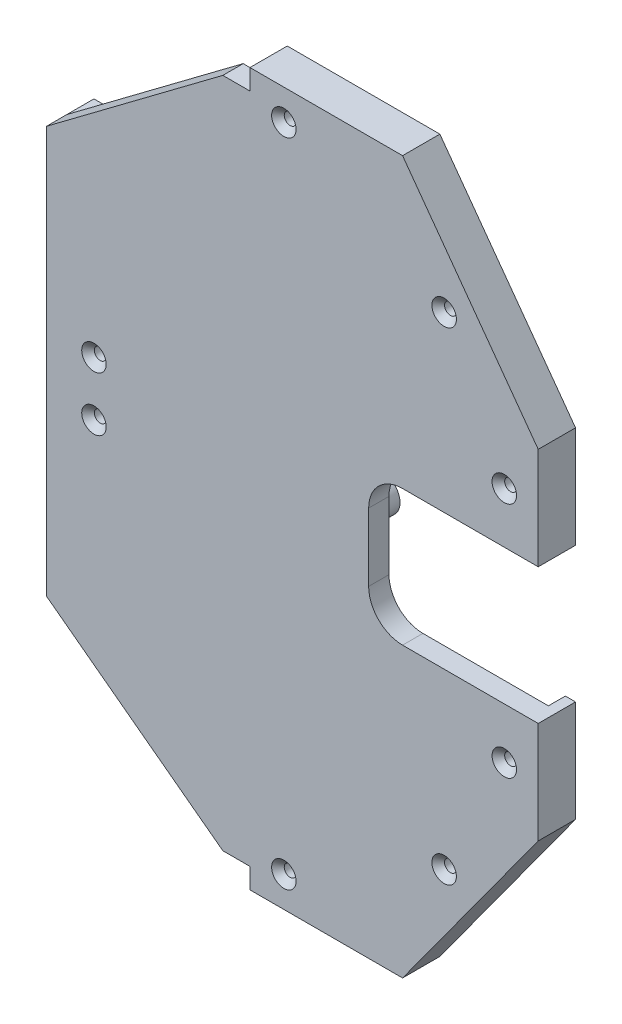
SolidWorks part; units mm, degrees
material "ABS PC"
ref_plane "Piano frontale" through (0, 0, 0) normal (0, 0, 1) x (1, 0, 0)
ref_plane "Piano superiore" through (0, 0, 0) normal (0, 1, 0) x (1, 0, 0)
ref_plane "Piano destro" through (0, 0, 0) normal (1, 0, 0) x (0, 0, -1)
sketch "Schizzo1" plane through (0, 0, 0) normal (0, 0, 1) x (1, 0, 0)
  line L0 (-8, -60) -> (-8, 60)
  line L1 (-8, 60) -> (52, 105)
  line L2 (52, 105) -> (97, 105)
  line L3 (97, 105) -> (137, 50)
  line L4 (137, 50) -> (137, -50)
  line L5 (0, 0) -> (30.0223, 0) construction
  line L6 (97, -105) -> (137, -50)
  line L7 (52, -105) -> (97, -105)
  line L8 (-8, -60) -> (52, -105)
  point P11 (137, 0)
  point P14 (-8, 0)
  dimension "D1" = 60
  dimension "D2" = 45
  dimension "D3" = 60
  dimension "D4" = 45
  dimension "D5" = 40
  dimension "D6" = 55
  dimension "D7" = 100
  dimension "D8" = 8
extrude "Estrusione-Estrusione2" add sketch "Schizzo1" along normal blind 6
shell "Svuota1" [suppressed] thickness 6
sketch "Schizzo2" plane through (0, 0, 0) normal (0, 0, -1) x (-1, 0, 0)
  line L6 (8, -60) -> (-17, -60)
  line L7 (8, -60) -> (8, -24)
  line L8 (8, -24) -> (-17, -24)
  line L9 (-17, -60) -> (-17, -24)
  line L10 (8, 60) -> (-17, 60)
  line L11 (8, 60) -> (8, 24)
  line L12 (8, 24) -> (-17, 24)
  line L13 (-17, 60) -> (-17, 24)
  dimension "D1" = 25
  dimension "D2" = 25
  dimension "D3" = 36
  dimension "D4" = 36
extrude "Estrusione-Estrusione3" add sketch "Schizzo2" along normal blind 8
sketch "Schizzo3" plane through (0, 0, 6) normal (0, 0, -1) x (-1, 0, 0)
  line L0 (-52, 105) -> (-44, 99)
  line L1 (-44, 99) -> (-52, 99)
  line L3 (-52, 99) -> (-52, 105)
  line L4 (-52, -105) -> (-44, -99)
  line L5 (-44, -99) -> (-52, -99)
  line L7 (-52, -99) -> (-52, -105)
  dimension "D1" = 6
  dimension "D2" = 8
  dimension "D3" = 6
  dimension "D4" = 8
extrude "Taglio-Estrusione1" cut sketch "Schizzo3" along normal through all
sketch "Schizzo4" plane through (0, 0, -8) normal (0, 0, -1) x (-1, 0, 0)
  line L0 (2.85, 30.0133) -> (2.85, 31.8867)
  line L1 (2.85, -30.0133) -> (2.85, -31.8867)
  arc A0 (2.85, 31.8867) -> (2.85, 30.0133) centre (0, 30.95) ccw
  arc A1 (2.85, -30.0133) -> (2.85, -31.8867) centre (0, -30.95) ccw
  dimension "D1" = 6
  dimension "D2" = 6
  dimension "D3" = 30.95
  dimension "D4" = 30.95
  dimension "D5" = 2.85
  dimension "D6" = 2.85
extrude "Taglio-Estrusione2" cut sketch "Schizzo4" against normal blind 10.5
sketch "Schizzo5" [suppressed] plane through (0, 0, 9) normal (0, 0, -1) x (-1, 0, 0)
  line L0 (-52, -99) -> (-93.9447, -99) construction
  line L1 (-93.9447, -99) -> (-131, -48.0489) construction
  line L2 (-131, -48.0489) -> (-131, 48.0489) construction
  line L3 (-131, 48.0489) -> (-93.9447, 99) construction
  line L4 (-93.9447, 99) -> (-52, 99) construction
  line L5 (-58, -99) -> (-66, -99)
  line L6 (-110.0355, -76.8751) -> (-114.7458, -70.3984)
  line L7 (-131, -39) -> (-131, -31)
  line L8 (-114.7458, 70.3984) -> (-110.0355, 76.8751)
  line L9 (-66, 99) -> (-58, 99)
  line L10 (-52, -99) -> (-52, -105) construction
  line L11 (-66, 95) -> (-66, 99)
  line L12 (-58, 95) -> (-58, 99)
  line L13 (-106.7654, 74.2608) -> (-110.0355, 76.8751)
  line L14 (-111.7607, 68.0121) -> (-114.7458, 70.3984)
  line L15 (-127, 39) -> (-131, 39)
  line L16 (-127, 31) -> (-131, 31)
  line L17 (-127, -31) -> (-131, -31)
  line L18 (-127, -39) -> (-131, -39)
  line L19 (-106.7654, -74.2608) -> (-110.0355, -76.8751)
  line L20 (-111.7607, -68.0121) -> (-114.7458, -70.3984)
  line L21 (-66, -95) -> (-66, -99)
  line L22 (-58, -95) -> (-58, -99)
  line L23 (-131, 31) -> (-131, 39)
  arc A0 (-66, 95) -> (-58, 95) centre (-62, 95) ccw
  arc A1 (-111.7607, 68.0121) -> (-106.7654, 74.2608) centre (-109.2631, 71.1365) ccw
  arc A2 (-127, 31) -> (-127, 39) centre (-127, 35) ccw
  arc A3 (-127, -39) -> (-127, -31) centre (-127, -35) ccw
  arc A4 (-106.7654, -74.2608) -> (-111.7607, -68.0121) centre (-109.2631, -71.1365) ccw
  arc A5 (-58, -95) -> (-66, -95) centre (-62, -95) ccw
  dimension "D1" = 8
  dimension "D5" = 8
  dimension "D7" = 4
  dimension "D9" = 15.3184
  dimension "D8" = 8
  dimension "D10" = 4
  dimension "D11" = 35
  dimension "D12" = 8
  dimension "D13" = 4
  dimension "D14" = 35
  dimension "D16" = 15.3184
  dimension "D17" = 8
  dimension "D18" = 4
  dimension "D19" = 8
  dimension "D20" = 10
  dimension "D2" = 41.9447
  dimension "D3" = 10
  dimension "D4" = 4
  dimension "D6" = 63.0009
  dimension "D15" = 4
extrude "Estrusione-Estrusione4" [suppressed] add sketch "Schizzo5" along normal up to surface (9 mm away)
sketch "Schizzo6" plane through (0, 0, 0) normal (0, 0, -1) x (-1, 0, 0)
  line L0 (-65, 0) -> (-75, 0) construction
  line L1 (-65, -3.25) -> (-75, -3.25)
  line L2 (-65, 3.25) -> (-75, 3.25)
  line L3 (-65, -5.25) -> (-75, -5.25)
  line L4 (-65, 5.25) -> (-75, 5.25)
  line L5 (-97.1925, 53.28) -> (-99.5884, 53.28)
  line L6 (-101.5884, 51.28) -> (-101.5884, 45.28)
  line L7 (-99.5884, 43.28) -> (-88.3384, 43.28)
  line L8 (-86.3384, 45.28) -> (-86.3384, 46.5885)
  line L9 (-87.7059, 48.4858) -> (-92.0679, 49.9399)
  line L10 (-97.1925, -53.28) -> (-99.5884, -53.28)
  line L11 (-101.5884, -51.28) -> (-101.5884, -45.28)
  line L12 (-99.5884, -43.28) -> (-88.3384, -43.28)
  line L13 (-86.3384, -45.28) -> (-86.3384, -46.5885)
  line L14 (-87.7059, -48.4858) -> (-92.0679, -49.9399)
  line L20 (-75.2704, -92.5997) -> (-79.6325, -94.0537)
  line L21 (-81, -95.951) -> (-81, -96.9595)
  line L22 (-79, -98.9595) -> (-71, -98.9595)
  line L23 (-67, -94.9595) -> (-67, -91.2595)
  line L24 (-69, -89.2595) -> (-70.1459, -89.2595)
  line L25 (-70.1459, 89.2595) -> (-69, 89.2595)
  line L26 (-67, 91.2595) -> (-67, 94.9595)
  line L27 (-71, 98.9595) -> (-79, 98.9595)
  line L28 (-81, 96.9595) -> (-81, 95.951)
  line L29 (-79.6325, 94.0537) -> (-75.2704, 92.5997)
  arc A0 (-65, -3.25) -> (-65, 3.25) centre (-65, 0) ccw
  arc A1 (-75, 3.25) -> (-75, -3.25) centre (-75, 0) ccw
  arc A2 (-75, 5.25) -> (-75, -5.25) centre (-75, 0) ccw
  arc A3 (-65, -5.25) -> (-65, 5.25) centre (-65, 0) ccw
  arc A4 (-75, 89.2595) -> (-92.3384, 53.28) centre (0, 30.95) ccw construction
  arc A5 (-77.5658, 91.2543) -> (-95.4973, 54.0439) centre (0, 30.95) ccw construction
  arc A6 (-72.4342, 87.2647) -> (-89.1794, 52.5161) centre (0, 30.95) ccw construction
  arc A7 (-72.4342, 87.2647) -> (-77.5658, 91.2543) centre (-75, 89.2595) ccw construction
  arc A8 (-95.4973, 54.0439) -> (-89.1794, 52.5161) centre (-92.3384, 53.28) ccw construction
  arc A9 (-95.3433, 52.0419) -> (-92.5625, 50.0377) centre (-92.3384, 53.28) ccw
  arc A10 (-79.1447, 92.4819) -> (-97.4413, 54.514) centre (0, 30.95) ccw construction
  arc A11 (-97.4413, 54.514) -> (-87.2354, 52.046) centre (-92.3384, 53.28) ccw construction
  arc A12 (-70.8553, 86.0372) -> (-87.2354, 52.046) centre (0, 30.95) ccw construction
  arc A13 (-70.8553, 86.0372) -> (-79.1447, 92.4819) centre (-75, 89.2595) ccw construction
  arc A14 (-75, -89.2595) -> (-92.3384, -53.28) centre (0, -30.95) cw construction
  arc A15 (-95.3433, 52.0419) -> (-97.1925, 53.28) centre (-97.1925, 51.28) ccw
  arc A16 (-99.5884, 53.28) -> (-101.5884, 51.28) centre (-99.5884, 51.28) ccw
  arc A21 (-95.4973, -54.0439) -> (-77.5658, -91.2543) centre (0, -30.95) ccw construction
  arc A22 (-89.1794, -52.5161) -> (-72.4342, -87.2647) centre (0, -30.95) ccw construction
  arc A23 (-89.1794, -52.5161) -> (-95.4973, -54.0439) centre (-92.3384, -53.28) ccw construction
  arc A24 (-77.5658, -91.2543) -> (-72.4342, -87.2647) centre (-75, -89.2595) ccw construction
  arc A25 (-97.4413, -54.514) -> (-79.1447, -92.4819) centre (0, -30.95) ccw construction
  arc A26 (-79.1447, -92.4819) -> (-70.8553, -86.0372) centre (-75, -89.2595) ccw construction
  arc A27 (-87.2354, -52.046) -> (-70.8553, -86.0372) centre (0, -30.95) ccw construction
  arc A28 (-87.2354, -52.046) -> (-97.4413, -54.514) centre (-92.3384, -53.28) ccw construction
  arc A29 (-101.5884, 45.28) -> (-99.5884, 43.28) centre (-99.5884, 45.28) ccw
  arc A30 (-88.3384, 43.28) -> (-86.3384, 45.28) centre (-88.3384, 45.28) ccw
  arc A31 (-86.3384, 46.5885) -> (-87.7059, 48.4858) centre (-88.3384, 46.5885) ccw
  arc A32 (-92.5625, 50.0377) -> (-92.0679, 49.9399) centre (-92.7004, 48.0425) cw
  arc A33 (-95.3433, -52.0419) -> (-92.5625, -50.0377) centre (-92.3384, -53.28) cw
  arc A34 (-88.3384, -43.28) -> (-86.3384, -45.28) centre (-88.3384, -45.28) cw
  arc A35 (-86.3384, -46.5885) -> (-87.7059, -48.4858) centre (-88.3384, -46.5885) cw
  arc A36 (-92.5625, -50.0377) -> (-92.0679, -49.9399) centre (-92.7004, -48.0425) ccw
  arc A37 (-95.3433, -52.0419) -> (-97.1925, -53.28) centre (-97.1925, -51.28) cw
  arc A38 (-99.5884, -53.28) -> (-101.5884, -51.28) centre (-99.5884, -51.28) cw
  arc A39 (-101.5884, -45.28) -> (-99.5884, -43.28) centre (-99.5884, -45.28) cw
  arc A47 (-71.9951, -90.4976) -> (-74.7759, -92.5018) centre (-75, -89.2595) cw
  arc A48 (-71, -98.9595) -> (-67, -94.9595) centre (-71, -94.9595) ccw
  arc A49 (-67, -91.2595) -> (-69, -89.2595) centre (-69, -91.2595) ccw
  arc A50 (-71.9951, -90.4976) -> (-70.1459, -89.2595) centre (-70.1459, -91.2595) cw
  arc A51 (-74.7759, -92.5018) -> (-75.2704, -92.5997) centre (-74.6379, -94.497) ccw
  arc A52 (-79.6325, -94.0537) -> (-81, -95.951) centre (-79, -95.951) ccw
  arc A53 (-81, -96.9595) -> (-79, -98.9595) centre (-79, -96.9595) ccw
  arc A54 (-71.9951, 90.4976) -> (-74.7759, 92.5018) centre (-75, 89.2595) ccw
  arc A55 (-69, 89.2595) -> (-67, 91.2595) centre (-69, 91.2595) ccw
  arc A56 (-71.9951, 90.4976) -> (-70.1459, 89.2595) centre (-70.1459, 91.2595) ccw
  arc A57 (-79, 98.9595) -> (-81, 96.9595) centre (-79, 96.9595) ccw
  arc A58 (-81, 95.951) -> (-79.6325, 94.0537) centre (-79, 95.951) ccw
  arc A59 (-74.7759, 92.5018) -> (-75.2704, 92.5997) centre (-74.6379, 94.497) cw
  arc A60 (-67, 94.9595) -> (-71, 98.9595) centre (-71, 94.9595) ccw
  point P3 (-70, 0)
  point P18 (-85.5813, 72.1912)
  point P36 (-85.5813, -72.1912)
  point P57 (-95.5884, 53.28)
  point P60 (-101.5884, 53.28)
  point P63 (-101.5884, 43.28)
  point P68 (-86.3384, 48.03)
  point P71 (-92.3384, 50.03)
  point P83 (-86.3384, -48.03)
  point P86 (-92.3384, -50.03)
  point P89 (-95.5884, -53.28)
  point P92 (-101.5884, -53.28)
  point P95 (-101.5884, -43.28)
  point P106 (-71.75, 89.2595)
  point P111 (-77.5617, 91.2595)
  point P112 (-81, 94.5095)
  point P115 (-75, 92.5095)
  point P132 (-71.75, -89.2595)
  point P135 (-75, -92.5095)
  point P138 (-81, -94.5095)
  dimension "D5" = 95
  dimension "D6" = 6.5
  dimension "D10" = 95
  dimension "D13" = 75
  dimension "D11" = 6.5
  dimension "D15" = 6
  dimension "D19" = 2
  dimension "D20" = 10
  dimension "D24" = 2
  dimension "D25" = 9.7
  dimension "D29" = 2
  dimension "D30" = 4
  dimension "D31" = 9.7
  dimension "D35" = 4
  dimension "D36" = 2
  dimension "D1" = 75
  dimension "D2" = 65
  dimension "D3" = 6.5
  dimension "D7" = 75
  dimension "D8" = 22.33
  dimension "D12" = 22.33
  dimension "D16" = 2
  dimension "D17" = 10
  dimension "D18" = 6
  dimension "D21" = 6
  dimension "D22" = 6
  dimension "D23" = 2
  dimension "D26" = 8
  dimension "D27" = 2
  dimension "D28" = 6
  dimension "D32" = 8
  dimension "D33" = 6
  dimension "D34" = 2
  dimension "D4" = 2
  dimension "D9" = 2
  dimension "D14" = 2
extrude "Estrusione-Estrusione5" add sketch "Schizzo6" along normal blind 10
sketch "Schizzo7" plane through (0, 0, 0) normal (0, 0, -1) x (-1, 0, 0)
  line L0 (-52, -105) -> (-97, -105) construction
  line L1 (-97, -105) -> (-137, -50) construction
  line L2 (-137, -50) -> (-137, 50) construction
  line L3 (-137, 50) -> (-97, 105) construction
  line L4 (-97, 105) -> (-52, 105) construction
  line L5 (-52, -105) -> (-97, -105)
  line L6 (-97, -105) -> (-137, -50)
  line L7 (-137, -50) -> (-137, 50)
  line L8 (-137, 50) -> (-97, 105)
  line L9 (-97, 105) -> (-52, 105)
  line L10 (-52, -102) -> (-95.4723, -102)
  line L11 (-95.4723, -102) -> (-134, -49.0244)
  line L12 (-134, -49.0244) -> (-134, 49.0244)
  line L13 (-134, 49.0244) -> (-95.4723, 102)
  line L14 (-95.4723, 102) -> (-52, 102)
  line L15 (-52, -102) -> (-52, -105)
  line L16 (-52, 105) -> (-52, 102)
  dimension "D1" = 3
extrude "Estrusione-Estrusione6" add sketch "Schizzo7" along normal blind 5
sketch "Schizzo8" plane through (0, 0, 6) normal (0, 0, 1) x (1, 0, 0)
  line L0 (137, -50) -> (137, 50) construction
  line L1 (137, 20) -> (97, 20)
  line L2 (137, 20) -> (137, -20)
  line L3 (137, -20) -> (97, -20)
  line L4 (87, 10) -> (87, -10)
  line L5 (52, 105) -> (52, 99) construction
  line L6 (137, 50) -> (97, 105) construction
  line L7 (97, 105) -> (52, 105) construction
  line L9 (52, -99) -> (52, -105) construction
  line L10 (97, -105) -> (137, -50) construction
  arc A0 (97, -20) -> (87, -10) centre (97, -10) cw
  arc A1 (97, 20) -> (87, 10) centre (97, 10) ccw
  arc A13 (58, 96) -> (66, 96) centre (62, 96) ccw construction
  circle A14 centre (62, 96) radius 1.75
  circle A15 centre (109.2631, 71.1365) radius 1.75
  circle A16 centre (127, 35) radius 1.75
  circle A17 centre (127, -35) radius 1.75
  circle A18 centre (109.2631, -71.1365) radius 1.75
  circle A19 centre (62, -96) radius 1.75
  circle A22 centre (6, -8) radius 1.75
  circle A23 centre (6, 8) radius 1.75
  point P11 (87, 20)
  dimension "D4" = 10
  dimension "D5" = 3.5
  dimension "D6" = 3.5
  dimension "D7" = 3.5
  dimension "D8" = 3.5
  dimension "D9" = 3.5
  dimension "D10" = 3.5
  dimension "D11" = 3.5
  dimension "D12" = 3.5
  dimension "D1" = 20
  dimension "D2" = 40
  dimension "D3" = 50
  dimension "D13" = 8
  dimension "D14" = 8
  dimension "D15" = 6
  dimension "D16" = 6
  dimension "D17" = 10
  dimension "D18" = 3
  dimension "D19" = 10
  dimension "D20" = 33.8635
  dimension "D21" = 10
  dimension "D22" = 35
  dimension "D23" = 35
  dimension "D24" = 10
  dimension "D25" = 3
  dimension "D26" = 10
  dimension "D27" = 10
  dimension "D28" = 33.8635
extrude "Taglio-Estrusione3" cut sketch "Schizzo8" against normal through all
sketch "Schizzo9" plane through (0, 0, 0) normal (0, 0, -1) x (-1, 0, 0)
  circle A0 centre (-60, 15.95) radius 3
  circle A1 centre (-60, 15.95) radius 5
  circle A2 centre (-60, -15.95) radius 3
  circle A3 centre (-60, -15.95) radius 5
  circle A5 centre (0, 30.95) radius 3 construction
  circle A6 centre (0, -30.95) radius 3 construction
  dimension "D1" = 10
  dimension "D2" = 6
  dimension "D3" = 10
  dimension "D4" = 6
  dimension "D7" = 15
  dimension "D5" = 60
  dimension "D6" = 60
  dimension "D8" = 15
extrude "Estrusione-Estrusione7" add sketch "Schizzo9" along normal blind 10
fillet "Raccordo1" radius 3 6 edges at (70, -5.25, 0) (80.25, 0, 0) (70, 5.25, 0) (55, -15.95, 0) (59.75, 0, 0) (55, 15.95, 0)
chamfer "Smusso1" distance 0.5 angle 45 8 edges at (78.25, 0, -10) (70, 3.25, -10) (61.75, 0, -10) (70, -3.25, -10) (57, -15.95, -10) (57, 15.95, -10) (3, -30.95, -8) (3, 30.95, -8)
chamfer "Smusso2" distance 1.86 angle 45 8 edges at (7.75, 8, 6) (7.75, -8, 6) (63.75, -96, 6) (111.0131, -71.1365, 6) (128.75, -35, 6) (128.75, 35, 6) (111.0131, 71.1365, 6) (63.75, 96, 6)
